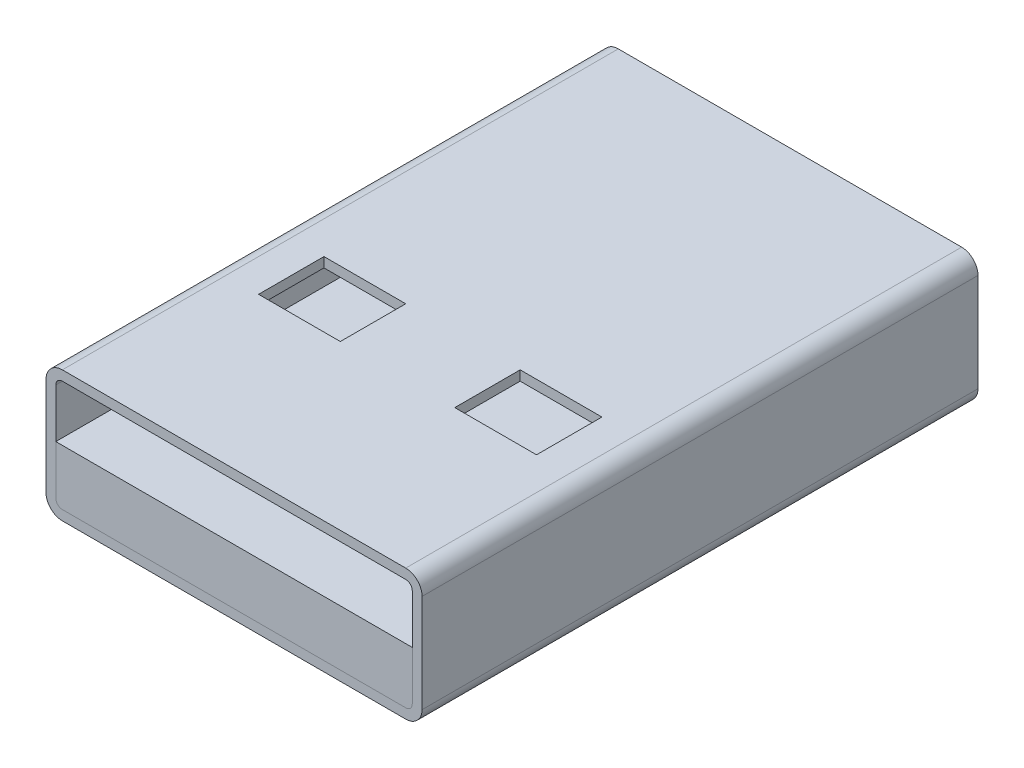
SolidWorks part; units mm, degrees
ref_plane "Спереди" through (0, 0, 0) normal (0, 0, 1) x (1, 0, 0)
ref_plane "Сверху" through (0, 0, 0) normal (0, 1, 0) x (1, 0, 0)
ref_plane "Справа" through (0, 0, 0) normal (1, 0, 0) x (0, 0, -1)
sketch "Эскиз1" plane through (0, 0, 0) normal (0, 0, 1) x (1, 0, 0)
  line L1 (0, 0) -> (11.5, 0)
  line L2 (0, 0) -> (0, 4)
  line L3 (0, 4) -> (11.5, 4)
  line L4 (11.5, 0) -> (11.5, 4)
  dimension "D1" = 4
  dimension "D2" = 11.5
extrude "Вытянуть1" add sketch "Эскиз1" along normal blind 17
fillet "Скругление1" radius 0.5 4 edges at (11.5, 4, 8.5) (11.5, 0, 8.5) (0, 0, 8.5) (0, 4, 8.5)
sketch "Эскиз2" plane through (0, 0, 17) normal (0, 0, 1) x (1, 0, 0)
  line L12 (11.2, 0.5) -> (11.2, 3.5)
  line L13 (11, 3.7) -> (0.5, 3.7)
  line L14 (0.3, 3.5) -> (0.3, 0.5)
  line L15 (0.5, 0.3) -> (11, 0.3)
  line L16 (11.2, 0.5) -> (11.2, 3.5)
  line L17 (11, 3.7) -> (0.5, 3.7)
  line L18 (0.3, 3.5) -> (0.3, 0.5)
  line L19 (0.5, 0.3) -> (11, 0.3)
  arc A10 (11.2, 3.5) -> (11, 3.7) centre (11, 3.5) ccw
  arc A11 (0.5, 3.7) -> (0.3, 3.5) centre (0.5, 3.5) ccw
  arc A12 (0.3, 0.5) -> (0.5, 0.3) centre (0.5, 0.5) ccw
  arc A13 (11, 0.3) -> (11.2, 0.5) centre (11, 0.5) ccw
  arc A14 (11.2, 3.5) -> (11, 3.7) centre (11, 3.5) ccw
  arc A15 (0.5, 3.7) -> (0.3, 3.5) centre (0.5, 3.5) ccw
  arc A16 (0.3, 0.5) -> (0.5, 0.3) centre (0.5, 0.5) ccw
  arc A17 (11, 0.3) -> (11.2, 0.5) centre (11, 0.5) ccw
  dimension "D1" = 0.3
extrude "Вырез-Вытянуть1" cut sketch "Эскиз2" against normal through all
sketch "Эскиз4" plane through (0, 4, 0) normal (0, 1, 0) x (1, 0, 0)
  line L0 (5.75, -17) -> (5.75, 0) construction
  line L1 (1.5, -10) -> (4, -10)
  line L2 (1.5, -10) -> (1.5, -12)
  line L3 (1.5, -12) -> (4, -12)
  line L4 (4, -10) -> (4, -12)
  line L5 (11, -17) -> (0.5, -17) construction
  line L6 (11, 0) -> (0.5, 0) construction
  line L7 (0, -17) -> (0, 0) construction
  line L8 (7.5, -10) -> (7.5, -12)
  line L9 (10, -12) -> (7.5, -12)
  line L10 (10, -10) -> (10, -12)
  line L11 (10, -10) -> (7.5, -10)
  dimension "D1" = 2
  dimension "D2" = 2.5
  dimension "D3" = 5
  dimension "D4" = 1.5
extrude "Вырез-Вытянуть2" cut sketch "Эскиз4" against normal through all
sketch "Эскиз3" plane through (0, 0, 17) normal (0, 0, 1) x (1, 0, 0)
  line L2 (11.2, 0.5) -> (11.2, 3.5) construction
  line L5 (0.5, 0.3) -> (11, 0.3) construction
  line L6 (0.3, 3.5) -> (0.3, 0.5) construction
  line L7 (11.2, 0.5) -> (11.2, 2)
  line L8 (0.5, 0.3) -> (11, 0.3)
  line L9 (0.3, 2) -> (0.3, 0.5)
  line L10 (0.3, 2) -> (11.2, 2)
  arc A2 (11, 0.3) -> (11.2, 0.5) centre (11, 0.5) ccw construction
  arc A3 (0.3, 0.5) -> (0.5, 0.3) centre (0.5, 0.5) ccw construction
  arc A4 (11, 0.3) -> (11.2, 0.5) centre (11, 0.5) ccw
  arc A5 (0.3, 0.5) -> (0.5, 0.3) centre (0.5, 0.5) ccw
extrude "Вытянуть2" add sketch "Эскиз3" against normal through all separate body
